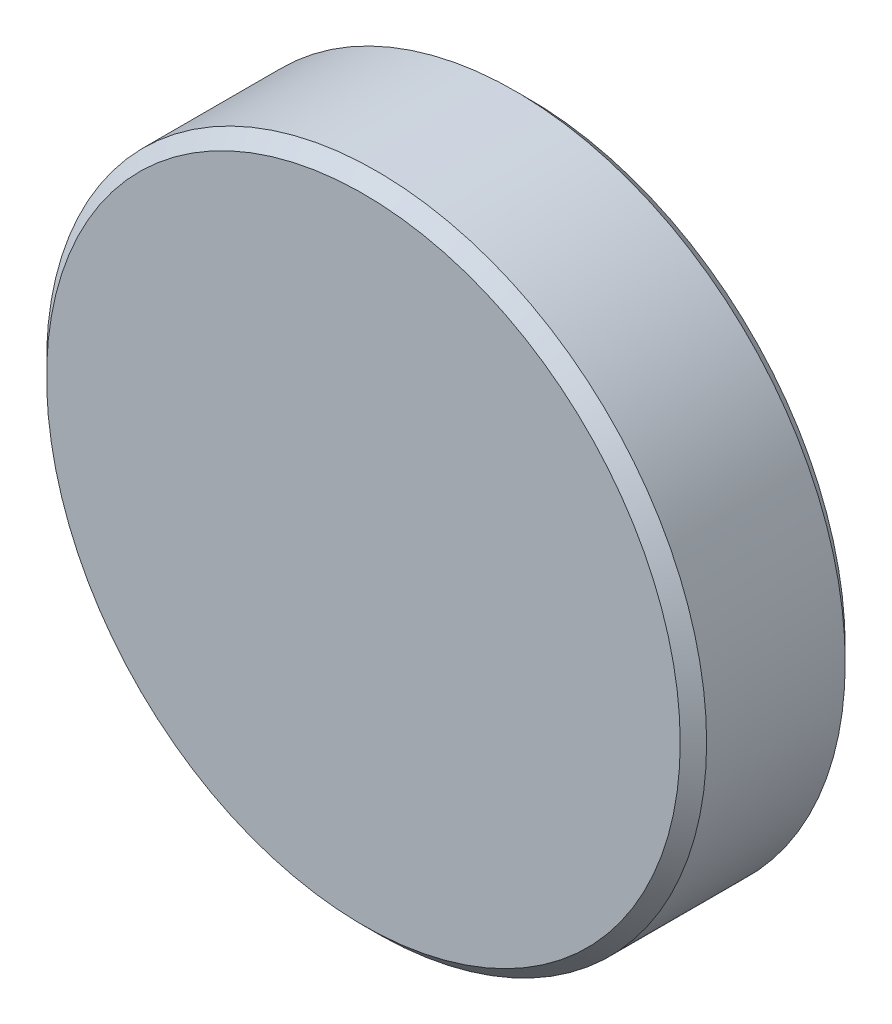
SolidWorks part; units mm, degrees
ref_plane "Plan de face" through (0, 0, 0) normal (0, 0, 1) x (1, 0, 0)
ref_plane "Plan de dessus" through (0, 0, 0) normal (0, 1, 0) x (1, 0, 0)
ref_plane "Plan de droite" through (0, 0, 0) normal (1, 0, 0) x (0, 0, -1)
sketch "Esquisse1" plane through (0, 0, 0) normal (0, 0, 1) x (1, 0, 0)
  circle A0 centre (0, 0) radius 100
  dimension "D1" = 200
extrude "Boss.-Extru.1" add sketch "Esquisse1" along normal blind 50
chamfer "Chanfrein1" distance 4 angle 45 1 edges at (100, 0, 0)
chamfer "Chanfrein2" distance 4 angle 45 1 edges at (100, 0, 50)
